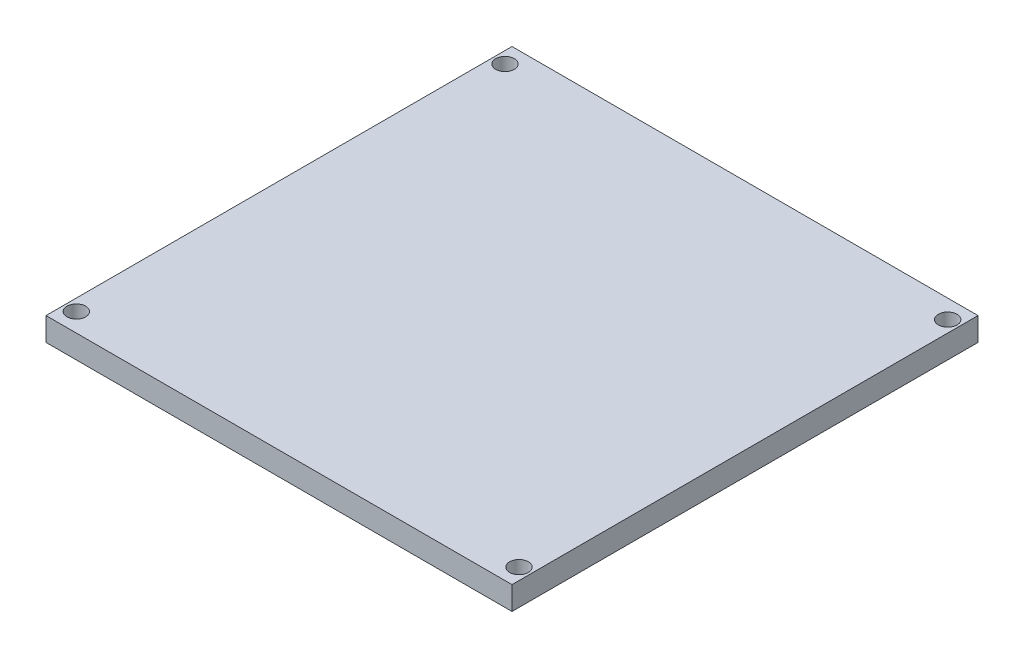
SolidWorks part; units mm, degrees
ref_plane "Front Plane" through (0, 0, 0) normal (0, 0, 1) x (1, 0, 0)
ref_plane "Top Plane" through (0, 0, 0) normal (0, 1, 0) x (1, 0, 0)
ref_plane "Right Plane" through (0, 0, 0) normal (1, 0, 0) x (0, 0, -1)
sketch "Sketch1" plane through (0, 0, 0) normal (0, 1, 0) x (1, 0, 0)
  line L1 (50, -50) -> (-50, -50)
  line L2 (50, -50) -> (50, 50)
  line L3 (50, 50) -> (-50, 50)
  line L4 (-50, -50) -> (-50, 50)
  line L5 (50, -50) -> (-50, 50) construction
  line L6 (50, 50) -> (-50, -50) construction
  point P0 (0, 0)
  dimension "D1" = 100
  dimension "D2" = 100
extrude "Boss-Extrude1" add sketch "Sketch1" along normal blind 5
hole_wizard "Ø4.0mm Dowel Hole1" positions "3DSketch3" profile "Sketch5" hole size "Ø4.0" standard "ISO" end condition up to next
sketch3d "3DSketch3"
  line L0 (-50, 5, -50) -> (-50, 5, 50) construction
  line L1 (50, 5, -50) -> (-50, 5, -50) construction
  line L2 (50, 5, 50) -> (50, 5, -50) construction
  line L3 (-50, 5, 50) -> (50, 5, 50) construction
  point P0 (-47.5, 5, -46)
  point P2 (47.5, 5, -46)
  point P4 (47.5, 5, 46)
  point P6 (-47.5, 5, 46)
  dimension "D1" = 2.5
  dimension "D2" = 4
  dimension "D3" = 2.5
  dimension "D4" = 4
  dimension "D5" = 2.5
  dimension "D6" = 4
  dimension "D7" = 2.5
  dimension "D8" = 4
sketch "Sketch5" plane through (-47.5, 5, -46) normal (1, 0, 0) x (0, 0, 1)
  line L0 (0, 0) -> (0, 5)
  line L1 (0, 5) -> (2, 5)
  line L2 (2, 5) -> (2, 0)
  line L5 (2, 0) -> (0, 0)
  line L11 (0, -6.35) -> (0, 107.95) construction
  dimension "Thru Hole Dia." = 4
  dimension "Thru Hole Depth" = 5
